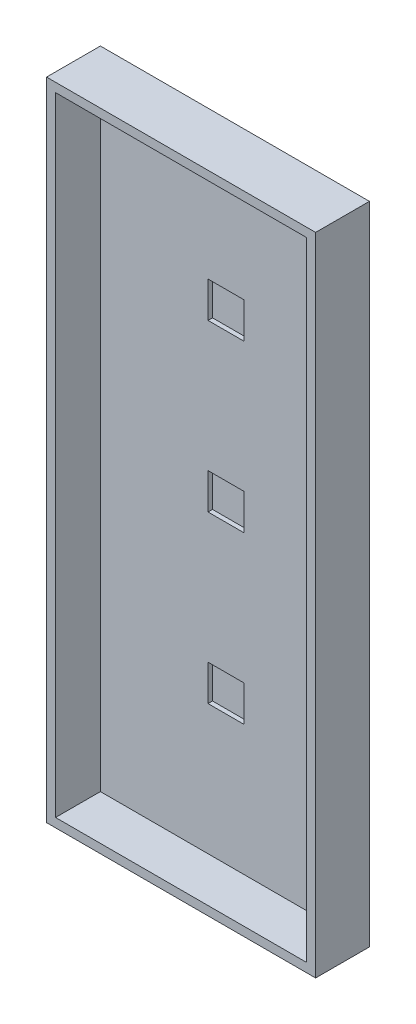
SolidWorks part; units mm, degrees
ref_plane "Front Plane" through (0, 0, 0) normal (0, 0, 1) x (1, 0, 0)
ref_plane "Top Plane" through (0, 0, 0) normal (0, 1, 0) x (1, 0, 0)
ref_plane "Right Plane" through (0, 0, 0) normal (1, 0, 0) x (0, 0, -1)
sketch "Sketch1" plane through (0, 0, 0) normal (0, 0, 1) x (1, 0, 0)
  line L1 (-1879.701, 750.8941) -> (-1117.701, 750.8941)
  line L2 (-1879.701, 750.8941) -> (-1879.701, -1077.9059)
  line L3 (-1879.701, -1077.9059) -> (-1117.701, -1077.9059)
  line L4 (-1117.701, 750.8941) -> (-1117.701, -1077.9059)
  point P6 (-2017.4633, 963.182)
  dimension "D1" = 1828.8
  dimension "D2" = 762
extrude "Boss-Extrude1" add sketch "Sketch1" along normal blind 152.4
sketch "Sketch2" plane through (0, 0, 152.4) normal (0, 0, 1) x (1, 0, 0)
  line L0 (-1879.701, 750.8941) -> (-1879.701, -1077.9059) construction
  line L1 (-1854.301, 725.4941) -> (-1143.101, 725.4941)
  line L2 (-1854.301, 725.4941) -> (-1854.301, -1052.5059)
  line L3 (-1854.301, -1052.5059) -> (-1143.101, -1052.5059)
  line L4 (-1143.101, 725.4941) -> (-1143.101, -1052.5059)
  line L5 (-1117.701, -1077.9059) -> (-1117.701, 750.8941) construction
  line L6 (-1117.701, 750.8941) -> (-1879.701, 750.8941) construction
  line L7 (-1879.701, -1077.9059) -> (-1117.701, -1077.9059) construction
  line L8 (-1549.501, -112.7059) -> (-1447.901, -112.7059)
  line L9 (-1549.501, 357.1941) -> (-1447.901, 357.1941)
  line L10 (-1549.501, 357.1941) -> (-1549.501, 255.5941)
  line L11 (-1549.501, 255.5941) -> (-1447.901, 255.5941)
  line L12 (-1447.901, 357.1941) -> (-1447.901, 255.5941)
  line L13 (-1549.501, -112.7059) -> (-1549.501, -214.3059)
  line L14 (-1549.501, -214.3059) -> (-1447.901, -214.3059)
  line L15 (-1447.901, -112.7059) -> (-1447.901, -214.3059)
  line L16 (-1549.501, -582.6059) -> (-1447.901, -582.6059)
  line L17 (-1549.501, -582.6059) -> (-1549.501, -684.2059)
  line L18 (-1549.501, -684.2059) -> (-1447.901, -684.2059)
  line L19 (-1447.901, -582.6059) -> (-1447.901, -684.2059)
  point P12 (0, 0)
  point P18 (0, 0)
  dimension "D1" = 25.4
  dimension "D2" = 25.4
  dimension "D3" = 25.4
  dimension "D4" = 25.4
  dimension "D5" = 101.6
  dimension "D6" = 101.6
  dimension "D7" = 304.8
  dimension "D8" = 368.3
  dimension "D9" = 3
sketch "Sketch5" plane through (0, 0, 152.4) normal (0, 0, 1) x (1, 0, 0)
extrude "Cut-Extrude3" cut sketch "Sketch2" against normal blind 127 contours L1 L4 L3 L2
sketch "Sketch10" plane through (0, 0, 25.4) normal (0, 0, 1) x (1, 0, 0)
  line L0 (-1854.301, 725.4941) -> (-1854.301, -1052.5059) construction
  line L1 (-1549.501, 357.1941) -> (-1447.901, 357.1941)
  line L2 (-1549.501, 357.1941) -> (-1549.501, 255.5941)
  line L3 (-1549.501, 255.5941) -> (-1447.901, 255.5941)
  line L4 (-1447.901, 357.1941) -> (-1447.901, 255.5941)
  line L5 (-1854.301, 725.4941) -> (-1143.101, 725.4941) construction
  line L6 (-1549.501, -112.7059) -> (-1549.501, -214.3059)
  line L7 (-1549.501, -112.7059) -> (-1447.901, -112.7059)
  line L8 (-1447.901, -112.7059) -> (-1447.901, -214.3059)
  line L9 (-1549.501, -214.3059) -> (-1447.901, -214.3059)
  line L10 (-1549.501, -582.6059) -> (-1549.501, -684.2059)
  line L11 (-1549.501, -582.6059) -> (-1447.901, -582.6059)
  line L12 (-1447.901, -582.6059) -> (-1447.901, -684.2059)
  line L13 (-1549.501, -684.2059) -> (-1447.901, -684.2059)
  dimension "D1" = 101.6
  dimension "D2" = 101.6
  dimension "D3" = 304.8
  dimension "D4" = 368.3
  dimension "D5" = 3
extrude "Cut-Extrude4" cut sketch "Sketch10" against normal blind 12.7
